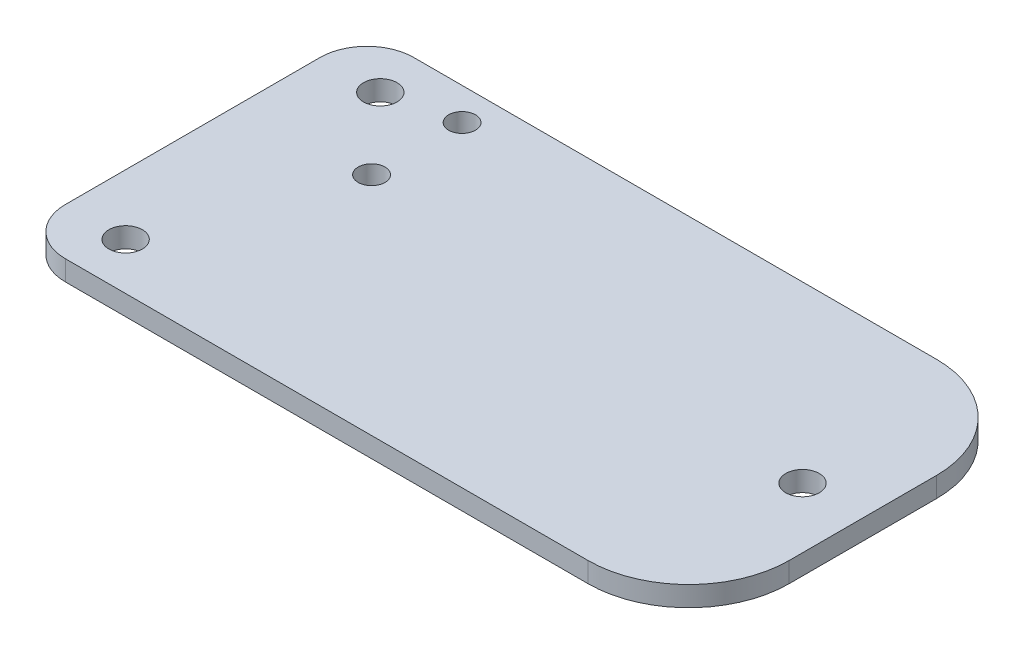
SolidWorks part; units mm, degrees
ref_plane "Front Plane" through (0, 0, 0) normal (0, 0, 1) x (1, 0, 0)
ref_plane "Top Plane" through (0, 0, 0) normal (0, 1, 0) x (1, 0, 0)
ref_plane "Right Plane" through (0, 0, 0) normal (1, 0, 0) x (0, 0, -1)
sketch "Sketch1" plane through (0, 0, 0) normal (0, 1, 0) x (1, 0, 0)
  line L0 (-41, -19) -> (-41, 19)
  line L1 (-50, 26) -> (50, 26)
  line L2 (-50, 26) -> (-50, -26)
  line L3 (-50, -26) -> (50, -26)
  line L4 (50, 26) -> (50, -26)
  line L5 (-50, 26) -> (50, -26) construction
  line L6 (-50, -26) -> (50, 26) construction
  circle A0 centre (41, 0) radius 2.5
  circle A1 centre (-41, 19) radius 2.5
  circle A2 centre (-41, -19) radius 2.5
  circle A3 centre (-31, 21.2) radius 2
  circle A4 centre (-31, 7.7) radius 2
  point P0 (0, 0)
  point P12 (-41, 0)
  point P17 (0, 0)
  point P18 (-31, 21.2)
  dimension "D6" = 5
  dimension "D10" = 4
  dimension "D1" = 52
  dimension "D2" = 100
  dimension "D3" = 38
  dimension "D4" = 9
  dimension "D5" = 9
  dimension "D7" = 13.5
  dimension "D8" = 4.8
  dimension "D9" = 19
extrude "Boss-Extrude1" add sketch "Sketch1" along normal blind 3
fillet "Fillet1" radius 15 2 edges at (50, 1.5, -26) (50, 1.5, 26)
fillet "Fillet2" radius 7 2 edges at (-50, 1.5, 26) (-50, 1.5, -26)
